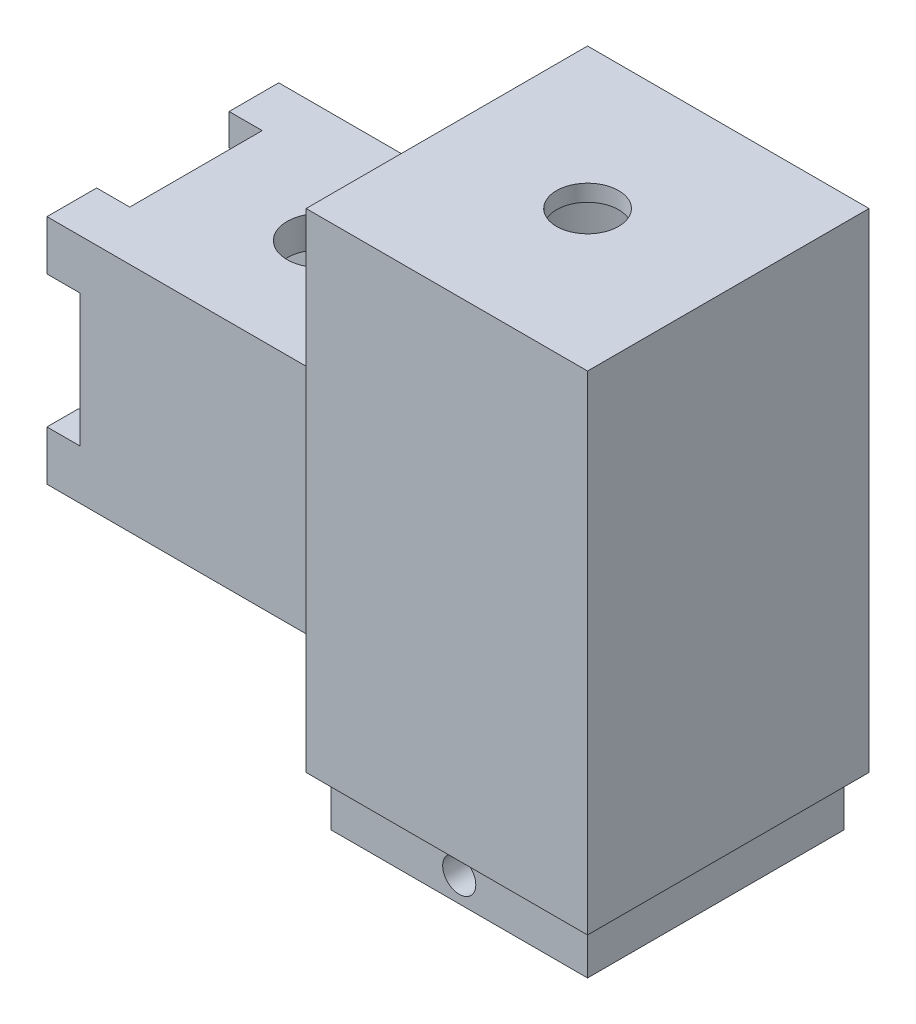
SolidWorks part; units mm, degrees
ref_plane "Alzado" through (0, 0, 0) normal (0, 0, 1) x (1, 0, 0)
ref_plane "Planta" through (0, 0, 0) normal (0, 1, 0) x (1, 0, 0)
ref_plane "Vista lateral" through (0, 0, 0) normal (1, 0, 0) x (0, 0, -1)
sketch "Croquis1" plane through (0, 0, 0) normal (1, 0, 0) x (0, 0, -1)
  line L1 (-14, 14) -> (14, 14)
  line L2 (-14, 14) -> (-14, -14)
  line L3 (-14, -14) -> (14, -14)
  line L4 (14, 14) -> (14, -14)
  line L5 (-14, 14) -> (14, -14) construction
  line L6 (-14, -14) -> (14, 14) construction
  line L7 (-10.2, 10.2) -> (10.2, 10.2)
  line L8 (-10.2, 10.2) -> (-10.2, -10.2)
  line L9 (-10.2, -10.2) -> (10.2, -10.2)
  line L10 (10.2, 10.2) -> (10.2, -10.2)
  line L11 (-10.2, 10.2) -> (10.2, -10.2) construction
  line L12 (-10.2, -10.2) -> (10.2, 10.2) construction
  point P0 (0, 0)
  point P6 (0, 0)
  dimension "D1" = 28
  dimension "D2" = 28
  dimension "D3" = 20.4
  dimension "D4" = 20.4
extrude "Saliente-Extruir1" add sketch "Croquis1" along normal blind 30.3
sketch "Croquis2" plane through (0, 0, 0) normal (0, 1, 0) x (1, 0, 0)
  line L0 (30.3, 0) -> (64.3, 0) construction
  line L1 (30.3, 14) -> (30.3, -14) construction
  line L3 (64.3, 17) -> (30.3, 17)
  line L4 (64.3, 17) -> (64.3, -17)
  line L5 (64.3, -17) -> (30.3, -17)
  line L6 (30.3, 17) -> (30.3, -17)
  line L7 (64.3, 17) -> (30.3, -17) construction
  line L8 (64.3, -17) -> (30.3, 17) construction
  point P5 (47.3, 0)
  dimension "D1" = 34
  dimension "D2" = 34
  dimension "D3" = 34
extrude "Saliente-Extruir2" add sketch "Croquis2" along normal mid plane 63
sketch "Croquis3" plane through (0, -31.5, 0) normal (0, -1, 0) x (1, 0, 0)
  line L0 (30.3, 0) -> (64.3, 0) construction
  line L1 (30.3, 14) -> (30.3, -14) construction
  line L2 (64.3, 17) -> (64.3, -17) construction
  circle A0 centre (47.3, 0) radius 12.625
  dimension "D1" = 25.25
extrude "Cortar-Extruir1" cut sketch "Croquis3" against normal blind 63
sketch "Croquis4" plane through (0, 31.5, 0) normal (0, 1, 0) x (1, 0, 0)
  line L0 (30.3, 0) -> (64.3, 0) construction
  line L1 (30.3, 17) -> (30.3, -17) construction
  line L2 (64.3, -17) -> (64.3, 17) construction
  line L4 (30.3, 17) -> (64.3, 17)
  line L5 (30.3, 17) -> (30.3, -17)
  line L6 (30.3, -17) -> (64.3, -17)
  line L7 (64.3, 17) -> (64.3, -17)
  line L8 (30.3, 17) -> (64.3, -17) construction
  line L9 (30.3, -17) -> (64.3, 17) construction
  point P6 (47.3, 0)
extrude "Saliente-Extruir3" add sketch "Croquis4" along normal blind 2
sketch "Croquis5" plane through (0, 33.5, 0) normal (0, 1, 0) x (1, 0, 0)
  line L0 (30.3, 0) -> (64.3, 0) construction
  line L1 (30.3, 17) -> (30.3, -17) construction
  line L2 (64.3, -17) -> (64.3, 17) construction
  circle A0 centre (47.3, 0) radius 3.75
  dimension "D1" = 7.5
extrude "Cortar-Extruir2" cut sketch "Croquis5" against normal up to next
sketch "Croquis6" plane through (30.3, 0, 0) normal (-1, 0, 0) x (0, 0, 1)
  line L0 (0, -31.5) -> (0, -20.5) construction
  line L1 (-17, -31.5) -> (17, -31.5) construction
  line L3 (-7.5, -20.5) -> (7.5, -20.5)
  line L4 (-7.5, -20.5) -> (-7.5, -31.5)
  line L5 (-7.5, -31.5) -> (7.5, -31.5)
  line L6 (7.5, -20.5) -> (7.5, -31.5)
  line L7 (-7.5, -20.5) -> (7.5, -31.5) construction
  line L8 (-7.5, -31.5) -> (7.5, -20.5) construction
  point P5 (0, -26)
  dimension "D1" = 11
  dimension "D2" = 15
extrude "Cortar-Extruir3" cut sketch "Croquis6" against normal up to next
sketch "Croquis7" plane through (0, -31.5, 0) normal (0, -1, 0) x (1, 0, 0)
  line L0 (47.3, 17) -> (47.3, -17) construction
  line L1 (30.3, 17) -> (64.3, 17) construction
  line L2 (64.3, -17) -> (30.3, -17) construction
  line L4 (30.3, 17) -> (64.3, 17)
  line L5 (30.3, 17) -> (30.3, -17)
  line L6 (30.3, -17) -> (64.3, -17)
  line L7 (64.3, 17) -> (64.3, -17)
  line L9 (30.3, -17) -> (64.3, 17) construction
  line L10 (31.8, 15.5) -> (62.8, 15.5)
  line L11 (31.8, 15.5) -> (31.8, -15.5)
  line L12 (31.8, -15.5) -> (62.8, -15.5)
  line L13 (62.8, 15.5) -> (62.8, -15.5)
  line L14 (31.8, 15.5) -> (62.8, -15.5) construction
  line L15 (31.8, -15.5) -> (62.8, 15.5) construction
  point P6 (47.3, 0)
  point P12 (47.3, 0)
  dimension "D1" = 31
  dimension "D2" = 31
extrude "Cortar-Extruir4" cut sketch "Croquis7" against normal blind 6
sketch "Croquis8" plane through (0, 0, 15.5) normal (0, 0, 1) x (1, 0, 0)
  line L0 (47.3, -25.5) -> (47.3, -31.5) construction
  line L1 (62.8, -25.5) -> (31.8, -25.5) construction
  line L2 (62.8, -31.5) -> (31.8, -31.5) construction
  circle A0 centre (47.3, -28.5) radius 2
  dimension "D1" = 4
extrude "Cortar-Extruir7" cut sketch "Croquis8" against normal blind 40
sketch "Croquis10" plane through (0, 14, 0) normal (0, 1, 0) x (1, 0, 0)
  line L0 (0, 0) -> (15, 0) construction
  circle A0 centre (15, 0) radius 4
  dimension "D2" = 8
  dimension "D1" = 15
extrude "Cortar-Extruir8" cut sketch "Croquis10" against normal blind 25.5
sketch "Croquis12" plane through (0, 0, 0) normal (-1, 0, 0) x (0, 0, 1)
  line L0 (10.2, 10.2) -> (10.2, -10.2) construction
  line L2 (14, 14) -> (14, 8)
  line L3 (14, 8) -> (10.2, 8)
  line L4 (10.2, 10.2) -> (10.2, 8)
  line L5 (-10.2, 10.2) -> (10.2, 10.2) construction
  line L6 (14, 14) -> (8, 14)
  line L7 (14, 14) -> (14, 10.2)
  line L8 (10.2, 10.2) -> (8, 10.2)
  line L9 (8, 14) -> (8, 10.2)
  line L10 (0, 0) -> (0, 14) construction
  line L11 (-14, 14) -> (14, 14) construction
  line L12 (0, 0) -> (14, 0) construction
  line L13 (14, 14) -> (14, -14) construction
  line L14 (14, -14) -> (8, -14)
  line L15 (8, -14) -> (8, -10.2)
  line L16 (10.2, -10.2) -> (8, -10.2)
  line L17 (10.2, -10.2) -> (10.2, -8)
  line L18 (14, -8) -> (10.2, -8)
  line L19 (14, -14) -> (14, -8)
  line L20 (-14, -14) -> (-14, -8)
  line L21 (-14, -8) -> (-10.2, -8)
  line L22 (-10.2, -10.2) -> (-10.2, -8)
  line L23 (-10.2, -10.2) -> (-8, -10.2)
  line L24 (-8, -14) -> (-8, -10.2)
  line L25 (-14, -14) -> (-8, -14)
  line L26 (-14, 14) -> (-8, 14)
  line L27 (-8, 14) -> (-8, 10.2)
  line L28 (-10.2, 10.2) -> (-8, 10.2)
  line L29 (-10.2, 10.2) -> (-10.2, 8)
  line L30 (-14, 8) -> (-10.2, 8)
  line L31 (-14, 14) -> (-14, 8)
  line M15 (-14, 14) -> (-14, -14)
  line M16 (-14, -14) -> (14, -14)
  line M17 (14, -14) -> (14, 14)
  line M18 (14, 14) -> (-14, 14)
  line M19 (-10.2, -10.2) -> (-10.2, 10.2)
  line M20 (-10.2, 10.2) -> (10.2, 10.2)
  line M21 (10.2, 10.2) -> (10.2, -10.2)
  line M22 (10.2, -10.2) -> (-10.2, -10.2)
  dimension "D1" = 6
  dimension "D2" = 6
extrude "Saliente-Extruir4" add sketch "Croquis12" along normal blind 4 contours L30 L27 M15 M19 M20 M18 | L9 L3 L2 M18 M20 M21 M17 | L18 L15 M17 M21 M22 M16 | L24 L21 M16 M22 M19 M15
